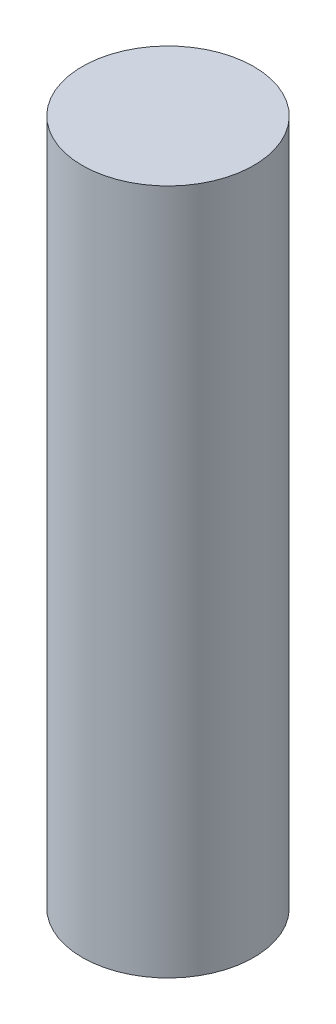
SolidWorks part; units mm, degrees
material "1060 Alloy"
ref_plane "Front Plane" through (0, 0, 0) normal (0, 0, 1) x (1, 0, 0)
ref_plane "Top Plane" through (0, 0, 0) normal (0, 1, 0) x (1, 0, 0)
ref_plane "Right Plane" through (0, 0, 0) normal (1, 0, 0) x (0, 0, -1)
sketch "Sketch1" plane through (0, 0, 0) normal (0, 1, 0) x (1, 0, 0)
  circle A0 centre (0, 0) radius 1.5875
  dimension "D1" = 3.175
extrude "Boss-Extrude1" add sketch "Sketch1" along normal blind 12.7
